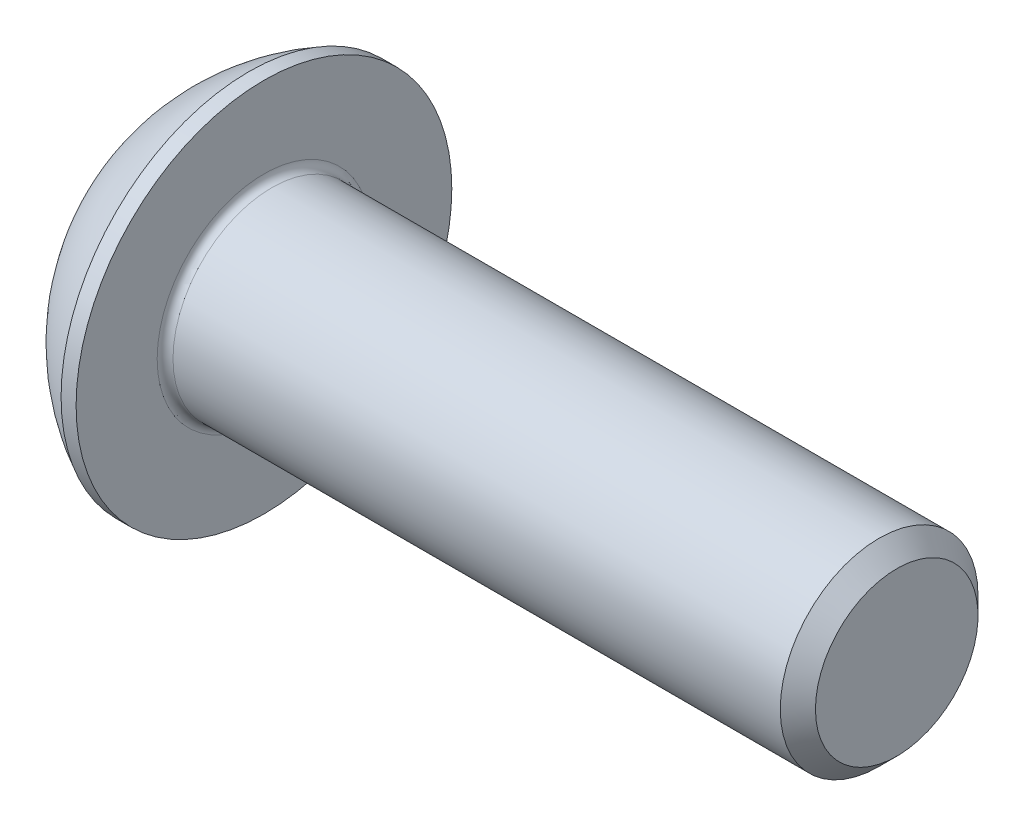
SolidWorks part; units mm, degrees
ref_plane "Plane1" through (0, 0, 0) normal (0, 0, 1) x (1, 0, 0)
ref_plane "Plane2" through (0, 0, 0) normal (0, 1, 0) x (1, 0, 0)
ref_plane "Plane3" through (0, 0, 0) normal (1, 0, 0) x (0, 0, -1)
sketch "BodySke" plane through (0, 0, 0) normal (0, 0, 1) x (1, 0, 0)
  line L0 (18.75, 0) -> (18.75, 2.055)
  line L1 (18.305, 2.5) -> (2.75, 2.5)
  line L2 (2.75, 2.5) -> (2.75, 4.75)
  line L3 (2.75, 4.75) -> (2.37, 4.75)
  line L4 (0, 0) -> (101.6, 0) construction
  line L5 (2.75, -4.75) -> (2.37, -4.75) construction
  line L6 (55.6768, -2.5) -> (2.75, -2.5) construction
  line L7 (18.75, 0) -> (0, 0)
  line L8 (0, 2.375) -> (0, -2.375) construction
  line L9 (0, 0) -> (0, 2.375)
  line L10 (18.75, 2.055) -> (18.305, 2.5)
  line L11 (18.75, -2.055) -> (18.305, -2.5) construction
  line L12 (3.55, 9.525) -> (3.55, -2.5) construction
  line L13 (2.75, 9.525) -> (2.75, -2.5) construction
  arc A1 (0, 2.375) -> (2.37, 4.75) centre (4.755, 0) cw
  dimension "Head_side_ht" = 0.38
  dimension "Body_ch_ang" = 45
revolve "BaseBody" add sketch "BodySke" angle 360 about L4
cosmetic thread "ThreadCosmetic" [suppressed] parameters "Thread_length"=14.4, "Thread_minor"=4.11
fillet "Fillet1" radius 0.2 1 edges at (2.75, 0, 2.5)
sketch "Sketch2" plane through (0, 0, 0) normal (0, 0, 1) x (1, 0, 0)
  line L0 (0, 1.5) -> (1.56, 1.5)
  line L1 (1.56, 1.5) -> (2.426, 0)
  line L3 (2.426, 0) -> (0, 0)
  line L4 (0, 0) -> (0, 1.5)
  line L5 (0, -1.5) -> (1.56, -1.5) construction
  line L6 (0, 0) -> (47.625, 0) construction
  dimension "D2" = 60
  dimension "PreBroach_depth" = 1.56
  dimension "PreBroach_dia" = 3
revolve "PreBroach" cut sketch "Sketch2" angle 360 about L6
sketch "Sketch3" plane through (0, 0, 0) normal (1, 0, 0) x (0, 0, -1)
  line L0 (-1.5, -0.866) -> (-1.5, 0.866)
  line L1 (-1.5, 0.866) -> (0, 1.7321)
  line L2 (0, 1.7321) -> (1.5, 0.866)
  line L3 (1.5, 0.866) -> (1.5, -0.866)
  line L4 (1.5, -0.866) -> (0, -1.7321)
  line L5 (0, -1.7321) -> (-1.5, -0.866)
  dimension "D1" = 1.5
  dimension "D2" = 1.5
extrude "Hex" cut sketch "Sketch3" along normal blind 1.56
sketch "ThdSchSke" plane through (0, 0, 0) normal (0, 0, 1) x (1, 0, 0)
  line L0 (4.35, -2.055) -> (4.0384, -2.5)
  line L1 (4.35, -2.055) -> (4.6616, -2.5)
  line L2 (4.6616, -2.5) -> (4.6616, -3.125)
  line L3 (-3.175, 0) -> (5.1513, 0) construction
  line L5 (4.6616, -3.125) -> (4.0384, -3.125)
  line L6 (4.0384, -3.125) -> (4.0384, -2.5)
  dimension "SideAngle" = 55
  dimension "VeeAngle" = 70
revolve "ThreadSchematic" [suppressed] cut sketch "ThdSchSke" angle 360 about L3
pattern_linear "ThdSchPat" [suppressed]
equation "\"D1@BodySke\" = \"Head_dia@BodySke\" * .5"
equation "\"Thread_minor@ThreadCosmetic\" = \"Minor_dia@BodySke\""
equation "\"D1@Sketch3\" = \"Hex_size@Sketch3\" / 2"
equation "\"D2@Sketch3\" = \"D1@Sketch3\""
equation "\"D3@Sketch3\" = \"Hex_size@Sketch3\""
equation "\"Thread_length@ThreadCosmetic\" = ((sgn( (\"Length@BodySke\" - \"Advance@BodySke\" * 2.0) - \"Thread_nom@BodySke\" )-1)*( (\"Length@BodySke\" - \"Advance@BodySke\" * 2.0) - \"Thread_nom@BodySke\" ))/-2+ \"Thread_nom@BodySke\""
equation "\"Thread_minor@ThdSchSke\" = \"Minor_dia@BodySke\""
equation "\"Diameter@ThdSchSke\" = \"Diameter@BodySke\""
equation "\"Overcut@ThdSchSke\" = \"Diameter@BodySke\" * 1.25"
equation "\"Start@ThdSchSke\" = \"Head_ht@BodySke\" + \"Length@BodySke\" - \"Thread_length@ThreadCosmetic\"  '---Non-countersunk---"
equation "\"Num_threads@ThdSchPat\" = int( \"Thread_length@ThreadCosmetic\" / \"Advance@BodySke\" + 0.999 )  + 1"
equation "\"Advance@ThdSchPat\" = \"Thread_length@ThreadCosmetic\" /  (\"Num_threads@ThdSchPat\" - 1) 'relax it"
equation "\"Num_threads@ThdSchPat\" = \"Num_threads@ThdSchPat\" - sgn( \"Num_threads@ThdSchPat\" - 1) '---chamfered tips only---"
